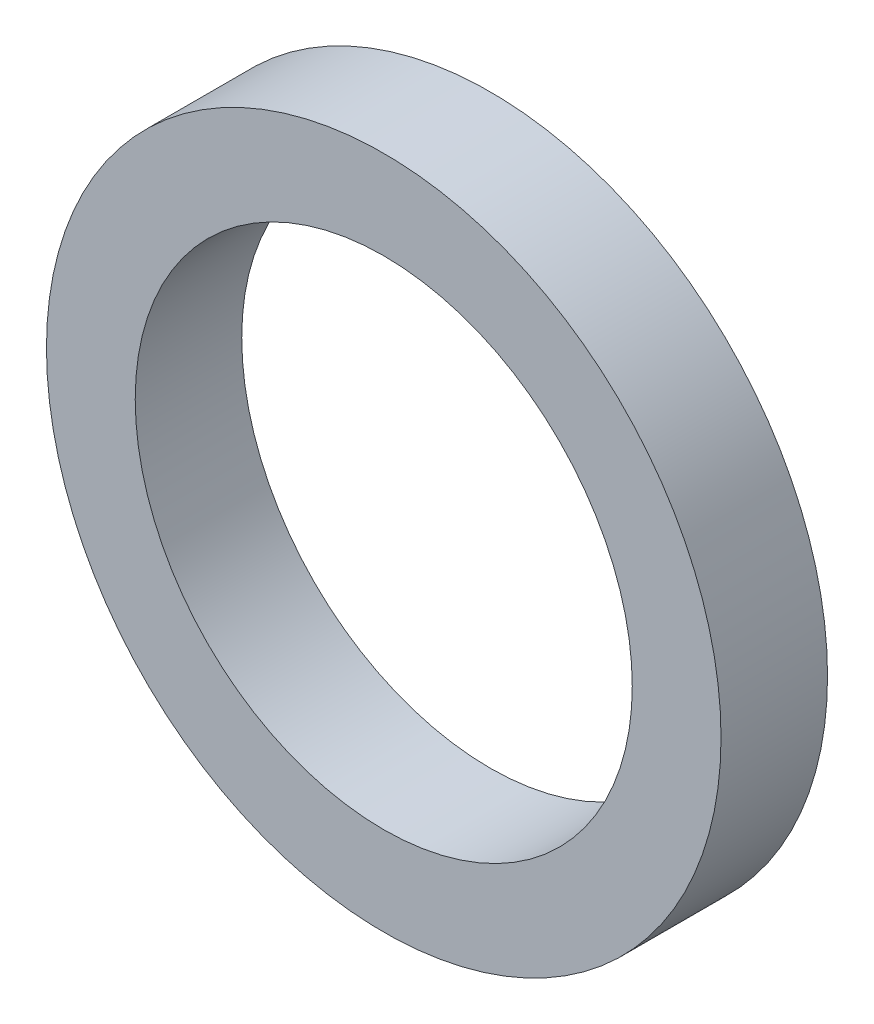
SolidWorks part; units mm, degrees
ref_plane "Piano frontale" through (0, 0, 0) normal (0, 0, 1) x (1, 0, 0)
ref_plane "Piano superiore" through (0, 0, 0) normal (0, 1, 0) x (1, 0, 0)
ref_plane "Piano destro" through (0, 0, 0) normal (1, 0, 0) x (0, 0, -1)
sketch "Schizzo1" plane through (0, 0, 0) normal (0, 0, 1) x (1, 0, 0)
  circle A0 centre (0, 0) radius 7
  circle A1 centre (0, 0) radius 9.5
extrude "Estrusione-Estrusione1" add sketch "Schizzo1" along normal blind 3
